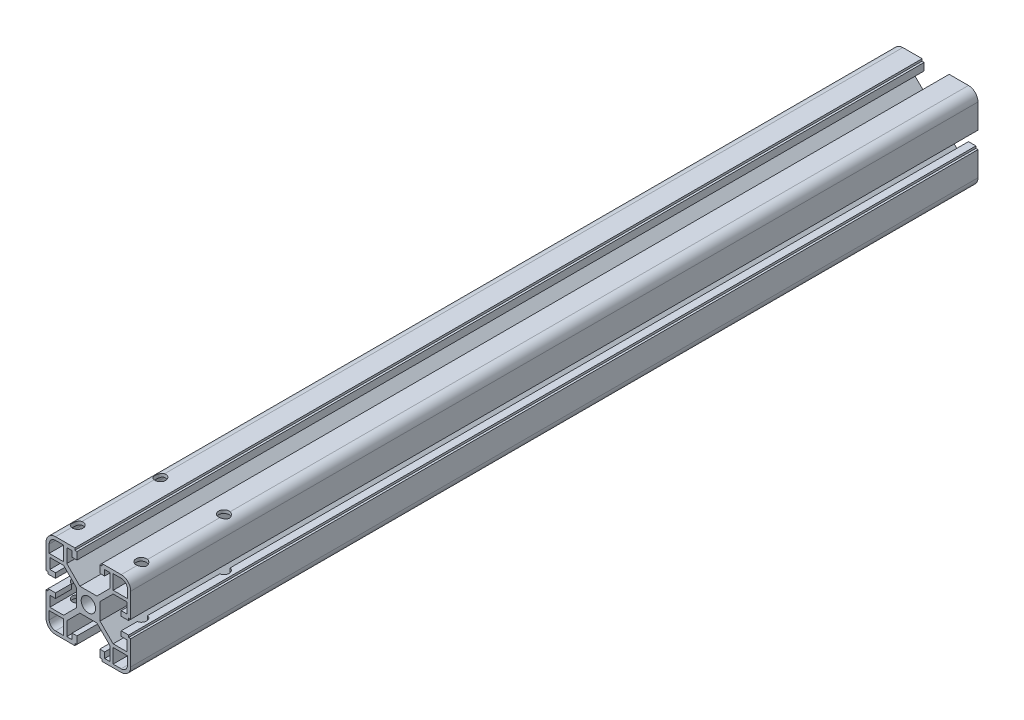
SolidWorks part; units mm, degrees
material "6061-T6 (SS)"
ref_plane "Front Plane" through (0, 0, 0) normal (0, 0, 1) x (1, 0, 0)
ref_plane "Top Plane" through (0, 0, 0) normal (0, 1, 0) x (1, 0, 0)
ref_plane "Right Plane" through (0, 0, 0) normal (1, 0, 0) x (0, 0, -1)
sketch "Sketch1" plane through (0, 0, 0) normal (0, 0, 1) x (1, 0, 0)
  line L0 (3.4, 0) -> (5.5, 0)
  line L1 (10.19, 11.69) -> (4, 5.5)
  line L2 (11.69, 10.19) -> (5.5, 4)
  line L3 (18.2, 10.19) -> (11.69, 10.19)
  line L4 (18.2, 10.19) -> (18.2, 5.2656)
  line L5 (18.2, 5.2656) -> (15.5, 5.2656)
  line L6 (15.5, 5.2656) -> (15.5, 2.9656)
  line L7 (15.5, 2.9656) -> (19, 2.9656)
  line L8 (19, 2.9656) -> (19, 3.9656)
  line L9 (19, 3.9656) -> (20, 3.9656)
  line L10 (20, 3.9656) -> (20, 15.5)
  line L11 (15.5, 20) -> (6.3853, 20)
  line L12 (18.5, 11.69) -> (18.5, 15.5)
  line L13 (15.5, 18.5) -> (11.69, 18.5)
  line L14 (11.69, 11.69) -> (11.69, 18.5)
  line L15 (0, 3.4) -> (0, 5.5)
  line L16 (4, 5.5) -> (0, 5.5)
  line L17 (6.3853, 20) -> (6.3853, 19)
  line L18 (5.5, 0) -> (5.5, 4)
  line L19 (6.3853, 19) -> (5.3853, 19)
  line L20 (5.3853, 19) -> (5.3853, 15.5)
  line L21 (5.3853, 15.5) -> (7.6853, 15.5)
  line L22 (10.19, 11.69) -> (10.19, 18.2)
  line L23 (11.69, 11.69) -> (18.5, 11.69)
  line L24 (7.6853, 18.2) -> (7.6853, 15.5)
  line L25 (10.19, 18.2) -> (7.6853, 18.2)
  arc A0 (20, 15.5) -> (15.5, 20) centre (15.5, 15.5) ccw
  arc A1 (18.5, 15.5) -> (15.5, 18.5) centre (15.5, 15.5) ccw
  arc A2 (3.4, 0) -> (0, 3.4) centre (0, 0) ccw
  dimension "D3" = 4.5
  dimension "D18" = 1.5
  dimension "D9" = 3.4
  dimension "D20" = 1.8
  dimension "D25" = 3
  dimension "D1" = 5.5
  dimension "D2" = 1.5
  dimension "D4" = 14.5
  dimension "D5" = 1.5
  dimension "D6" = 2.1
  dimension "D7" = 2.3
  dimension "D8" = 1.8
  dimension "D10" = 6.81
  dimension "D11" = 2.1
  dimension "D12" = 1
  dimension "D13" = 4.5
  dimension "D14" = 45
  dimension "D15" = 14.5
  dimension "D16" = 1
  dimension "D17" = 1.5
  dimension "D19" = 6.81
  dimension "D21" = 4.5
  dimension "D22" = 2.3
  dimension "D23" = 1
  dimension "D24" = 1
  dimension "D26" = 8.754
  dimension "D27" = 8.754
  dimension "D28" = 4.9244
  dimension "D29" = 2.5047
extrude "Boss-Extrude1" add sketch "Sketch1" along normal blind 400
mirror "Mirror1" about plane through (0, 0, 0) normal (0, 1, 0) of "Boss-Extrude1"
mirror "Mirror2" about plane through (0, 0, 0) normal (1, 0, 0) of "Boss-Extrude1"
mirror "Mirror3" about plane through (0, 0, 0) normal (0, 1, 0) of "Mirror2"
sketch "Sketch2" plane through (0, 5.5, 0) normal (0, 1, 0) x (1, 0, 0)
  line L0 (4, 0) -> (-4, 0) construction
  line L2 (-15, -351) -> (15, -351) construction
  line L3 (-15, -351) -> (-15, -390) construction
  line L4 (-15, -390) -> (15, -390) construction
  line L5 (15, -351) -> (15, -390) construction
  line L6 (-15, -351) -> (15, -390) construction
  line L7 (-15, -390) -> (15, -351) construction
  line L8 (4, -400) -> (-4, -400) construction
  circle A0 centre (0, -10) radius 2.5
  circle A1 centre (0, -60) radius 2.5
  circle A2 centre (-15, -351) radius 2.5
  circle A3 centre (15, -351) radius 2.5
  circle A4 centre (15, -390) radius 2.5
  circle A5 centre (-15, -390) radius 2.5
  point P7 (0, -370.5)
  dimension "D1" = 50
  dimension "D2" = 10
  dimension "D3" = 5
  dimension "D7" = 5
  dimension "D4" = 30
  dimension "D5" = 39
  dimension "D6" = 10
extrude "Cut-Extrude1" cut sketch "Sketch2" against normal through all both and the other way through all
